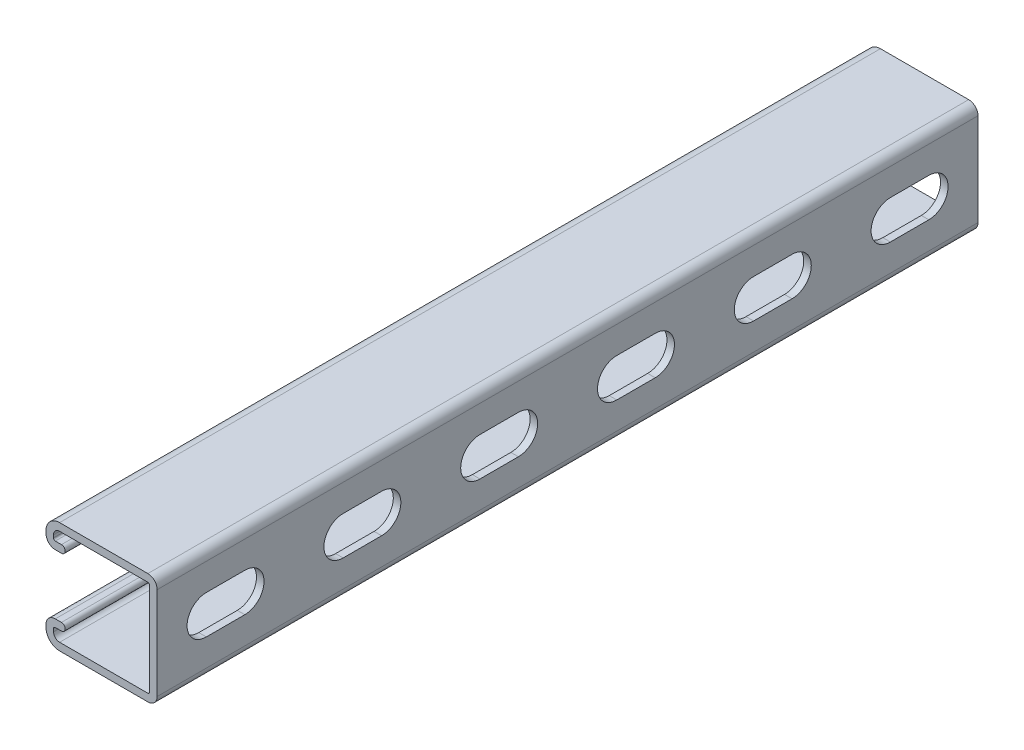
SolidWorks part; units mm, degrees
ref_plane "Front Plane" through (0, 0, 0) normal (0, 0, 1) x (1, 0, 0)
ref_plane "Top Plane" through (0, 0, 0) normal (0, 1, 0) x (1, 0, 0)
ref_plane "Right Plane" through (0, 0, 0) normal (1, 0, 0) x (0, 0, -1)
sketch "Sketch1" plane through (0, 0, 0) normal (0, 0, 1) x (1, 0, 0)
  line L0 (0, 0) -> (-41.275, 0) construction
  line L3 (-41.275, 20.6375) -> (0, 20.6375) construction
  line L4 (-41.275, 20.6375) -> (-41.275, -20.6375) construction
  line L5 (-41.275, -20.6375) -> (0, -20.6375) construction
  line L6 (0, 20.6375) -> (0, -20.6375) construction
  line L7 (-36.2267, 20.6375) -> (-3.4607, 20.6375)
  line L8 (0, 17.1767) -> (0, -17.1767)
  line L9 (-2.794, -17.1767) -> (-2.794, 17.1767)
  line L10 (-3.4608, 17.8435) -> (-36.2267, 17.8435)
  line L11 (-41.275, 15.5892) -> (-41.275, 14.5732)
  line L12 (-37.8142, 11.1125) -> (-35.5346, 11.1125)
  line L14 (-35.5346, 13.9065) -> (-37.8142, 13.9065)
  line L15 (-38.481, 14.5732) -> (-38.481, 15.5892)
  line L16 (-38.481, -14.5733) -> (-38.481, -15.5893)
  line L17 (-35.5346, -13.9065) -> (-37.8142, -13.9065)
  line L18 (-37.8142, -11.1125) -> (-35.5346, -11.1125)
  line L19 (-41.275, -15.5893) -> (-41.275, -14.5733)
  line L20 (-3.4607, -17.8435) -> (-36.2267, -17.8435)
  line L21 (-36.2267, -20.6375) -> (-3.4607, -20.6375)
  line L22 (-2.794, -20.6375) -> (-2.794, 20.6375) construction
  arc A1 (0, 17.1767) -> (-3.4607, 20.6375) centre (-3.4607, 17.1767) ccw
  arc A2 (-2.794, 17.1767) -> (-3.4608, 17.8435) centre (-3.4607, 17.1767) ccw
  arc A4 (-36.2267, 20.6375) -> (-41.275, 15.5892) centre (-36.2267, 15.5892) ccw
  arc A5 (-41.275, 14.5732) -> (-37.8142, 11.1125) centre (-37.8142, 14.5732) ccw
  arc A6 (-35.5346, 11.1125) -> (-35.5346, 13.9065) centre (-35.5346, 12.5095) ccw
  arc A7 (-37.8142, 13.9065) -> (-38.481, 14.5732) centre (-37.8142, 14.5732) cw
  arc A8 (-38.481, 15.5892) -> (-36.2267, 17.8435) centre (-36.2267, 15.5892) cw
  arc A9 (-38.481, -15.5893) -> (-36.2267, -17.8435) centre (-36.2267, -15.5893) ccw
  arc A10 (-37.8142, -13.9065) -> (-38.481, -14.5733) centre (-37.8142, -14.5733) ccw
  arc A11 (-35.5346, -11.1125) -> (-35.5346, -13.9065) centre (-35.5346, -12.5095) cw
  arc A12 (-41.275, -14.5733) -> (-37.8142, -11.1125) centre (-37.8142, -14.5733) cw
  arc A13 (-36.2267, -20.6375) -> (-41.275, -15.5893) centre (-36.2267, -15.5893) cw
  arc A14 (-2.794, -17.1767) -> (-3.4607, -17.8435) centre (-3.4607, -17.1767) cw
  arc A15 (0, -17.1767) -> (-3.4607, -20.6375) centre (-3.4607, -17.1767) cw
  point P24 (0, 20.6375)
  point P65 (-2.794, 0)
  dimension "D1" = 3.4608
  dimension "D2" = 5.0482
  dimension "D3" = 3.4608
  dimension "Ht." = 41.275
  dimension "Wd." = 41.275
  dimension "Thk." = 2.794
  dimension "D4" = 9.525
  dimension "D5" = 7.1374
extrude "Boss-Extrude1" add sketch "Sketch1" against normal blind 304.8
sketch "Sketch3" plane through (0, 0, 0) normal (1, 0, 0) x (0, 0, -1)
  line L0 (0, 0) -> (304.8, 0) construction
  point P2 (101.6, 0)
  point P3 (203.2, 0)
  dimension "D1" = 101.6
  dimension "D2" = 101.6
  dimension "D3" = 304.8
sketch "Sketch2" plane through (0, 0, 0) normal (1, 0, 0) x (0, 0, -1)
  line L0 (18.2562, 0) -> (32.5437, 0) construction
  line L1 (18.2562, 7.1438) -> (32.5437, 7.1438)
  line L2 (18.2562, -7.1438) -> (32.5437, -7.1438)
  line L3 (18.2562, 0) -> (0, 0) construction
  line L4 (25.4, 0) -> (76.2, 0) construction
  line L5 (0, -17.1767) -> (0, 17.1767) construction
  arc A0 (18.2562, 7.1438) -> (18.2562, -7.1438) centre (18.2562, 0) ccw
  arc A1 (32.5437, -7.1438) -> (32.5437, 7.1438) centre (32.5437, 0) ccw
  point P3 (25.4, 0)
  dimension "Slot Lg." = 28.575
  dimension "D2" = 25.4
  dimension "Slot Wd." = 14.2875
  dimension "Slot Ctr." = 50.8
  dimension "Hole to End" = 11.1125
extrude "Cut-Extrude1" cut sketch "Sketch2" against normal up to vertex (2.794 mm away) up to point (-2.794, 0, 0)
pattern_linear "LPattern1" count 6 spacing 50.8 along (0, 0, 1) of "Cut-Extrude1"
equation "\"D1@LPattern1\" = \"Slot Ctr.@Sketch2\""
equation "\"Hole Count@LPattern1\" = \"Lg.@Boss-Extrude1\" / \"D1@LPattern1\""
equation "\"D3@Sketch3\" = \"Lg.@Boss-Extrude1\""
